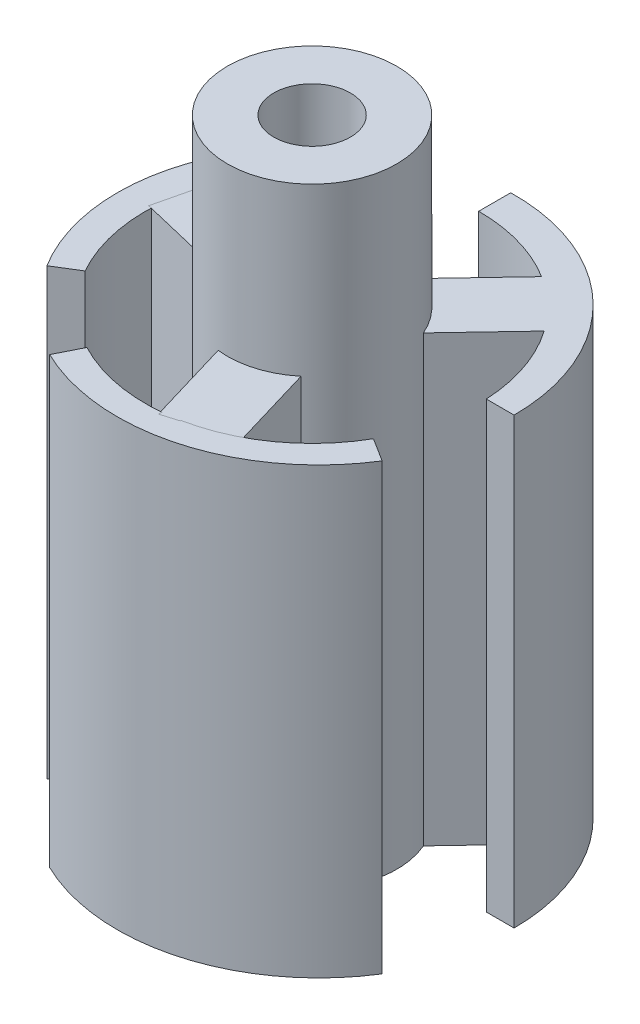
SolidWorks part; units mm, degrees
ref_plane "Front Plane" through (0, 0, 0) normal (0, 0, 1) x (1, 0, 0)
ref_plane "Top Plane" through (0, 0, 0) normal (0, 1, 0) x (1, 0, 0)
ref_plane "Right Plane" through (0, 0, 0) normal (1, 0, 0) x (0, 0, -1)
sketch "Sketch11" plane through (0, 0, 0) normal (0, 1, 0) x (1, 0, 0)
  line L0 (-15.1905, -8.6889) -> (0, 0.7002)
  line L1 (0, 0.7002) -> (-8.1366, -15.4934)
  line L2 (15.1201, -8.8109) -> (0, 0.7002)
  line L3 (0, 0.7002) -> (17.486, 0.7002)
  line L4 (0, 0.7002) -> (-9.3494, 14.7932)
  line L5 (0, 0.7002) -> (0, 17.8816)
  arc A3 (15.1201, -8.8109) -> (-8.1366, -15.4934) centre (-0.2456, 0.8547) cw
  arc A5 (-15.1905, -8.6889) -> (-9.3494, 14.7932) centre (-0.8078, 0.2009) cw
  arc A6 (17.486, 0.7002) -> (0, 17.8816) centre (0.3019, 0.7002) ccw
  circle A7 centre (0, 0.7002) radius 16.25
  point P11 (0, 0)
sketch "Sketch12" plane through (0, 0, 0) normal (0, 1, 0) x (1, 0, 0)
  circle A0 centre (0, 0) radius 15
extrude "Boss-Extrude6" add sketch "Sketch11" along normal blind 40 contours L0 A5 L4 | L2 A3 L1 | L3 A6 L5
extrude "Cut-Extrude9" cut sketch "Sketch12" along normal blind 40 contours A0
sketch "Sketch17" plane through (0, 0, 0) normal (0, 1, 0) x (1, 0, 0)
  line L0 (12.4951, 8.8245) -> (8.1399, 12.9515)
  line L1 (12.4951, 8.8245) -> (2.1256, -2.1183)
  line L2 (8.1399, 12.9515) -> (-2.2296, 2.0087)
  line L3 (2.1256, -2.1183) -> (-2.2296, 2.0087)
  line L4 (-2.8974, -0.7817) -> (2.8543, 0.9265)
  line L5 (1.3947, -15.2333) -> (-2.8974, -0.7817)
  line L6 (1.3947, -15.2333) -> (7.1464, -13.5251)
  line L7 (7.1464, -13.5251) -> (2.8543, 0.9265)
  line L8 (0.7717, 2.9) -> (-0.6248, -2.9352)
  line L9 (-13.8898, 6.4089) -> (0.7717, 2.9)
  line L10 (-13.8898, 6.4089) -> (-15.2863, 0.5736)
  line L11 (-15.2863, 0.5736) -> (-0.6248, -2.9352)
  arc A1 (14.9836, 0.7002) -> (0, 15) centre (0, 0) ccw construction
  point P18 (0, 0)
  dimension "D1" = 3
extrude "Boss-Extrude8" add sketch "Sketch17" along normal blind 40 separate body contours L2 L9 L8 L4 L7 L1 L0 | L4 L8 L3 L1 L7 | L9 L2 L3 L4 L8 | L11 L5 L6 L7 L1 L3 L8 | L5 L11 L8 L3 L4 | L10 L11 L5 L4 L3 L2 L9
sketch "Sketch18" plane through (0, 0, 0) normal (0, 1, 0) x (1, 0, 0)
  circle A0 centre (0, 0) radius 7.625
extrude "Boss-Extrude9" add sketch "Sketch18" along normal blind 55
sketch "Sketch22" plane through (0, 0, 0) normal (0, 1, 0) x (1, 0, 0)
  circle A0 centre (0, 0) radius 3.45
extrude "Cut-Extrude13" cut sketch "Sketch22" along normal through all
